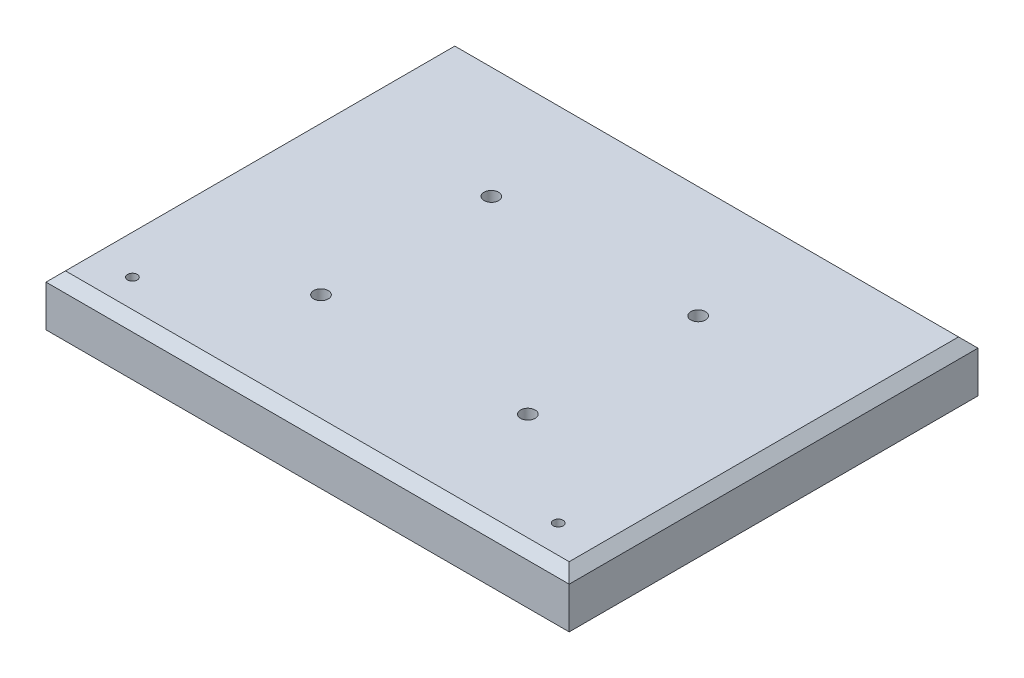
SolidWorks part; units mm, degrees
material "Oak"
ref_plane "Front Plane" through (0, 0, 0) normal (0, 0, 1) x (1, 0, 0)
ref_plane "Top Plane" through (0, 0, 0) normal (0, 1, 0) x (1, 0, 0)
ref_plane "Right Plane" through (0, 0, 0) normal (1, 0, 0) x (0, 0, -1)
sketch "Sketch1" plane through (0, 0, 0) normal (0, 1, 0) x (1, 0, 0)
  line L1 (0, 0) -> (215, 0)
  line L2 (0, 0) -> (0, 168)
  line L3 (0, 168) -> (215, 168)
  line L4 (215, 0) -> (215, 168)
  circle A0 centre (150, 118) radius 3
  circle A1 centre (65, 118) radius 3
  circle A2 centre (65, 48) radius 3
  circle A3 centre (150, 48) radius 3
  circle A4 centre (20, 15.5) radius 2
  circle A5 centre (195, 15.5) radius 2
  point P15 (0, 0)
  point P16 (0, 0)
  point P17 (0, 0)
  point P18 (0, 0)
  point P19 (0, 0)
  point P20 (0, 0)
  dimension "D3" = 65
  dimension "D11" = 20
  dimension "D1" = 168
  dimension "D2" = 215
  dimension "D4" = 65
  dimension "D5" = 50
  dimension "D6" = 50
  dimension "D7" = 70
  dimension "D8" = 65
  dimension "D9" = 65
  dimension "D10" = 70
  dimension "D12" = 175
  dimension "D13" = 32.5
  dimension "D14" = 32.5
extrude "Boss-Extrude1" add sketch "Sketch1" along normal blind 21
chamfer "Chamfer1" distance 4 angle 45 4 edges at (107.5, 21, -168) (0, 21, -84) (107.5, 21, 0) (215, 21, -84)
sketch "Sketch2" plane through (0, 0, 0) normal (0, -1, 0) x (1, 0, 0)
  circle A0 centre (65, -48) radius 9.5
  circle A1 centre (150, -48) radius 9.5
  circle A2 centre (65, -118) radius 9.5
  circle A3 centre (150, -118) radius 9.5
extrude "Cut-Extrude1" cut sketch "Sketch2" against normal blind 13
sketch "Sketch4" plane through (0, 0, 0) normal (0, -1, 0) x (1, 0, 0)
  circle A0 centre (20, -15.5) radius 5
  circle A1 centre (195, -15.5) radius 5
extrude "Cut-Extrude2" cut sketch "Sketch4" against normal blind 6.5
